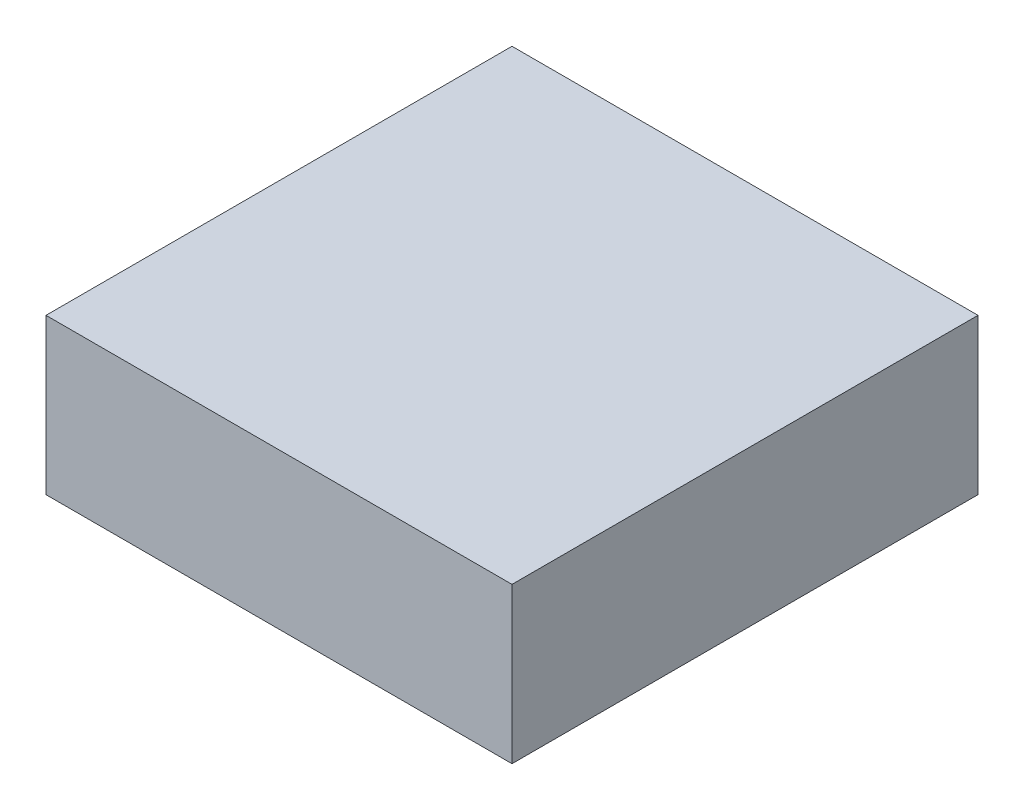
SolidWorks part; units mm, degrees
ref_plane "Alzado" through (0, 0, 0) normal (0, 0, 1) x (1, 0, 0)
ref_plane "Planta" through (0, 0, 0) normal (0, 1, 0) x (1, 0, 0)
ref_plane "Vista lateral" through (0, 0, 0) normal (1, 0, 0) x (0, 0, -1)
sketch "Croquis1" plane through (0, 0, 0) normal (0, 1, 0) x (1, 0, 0)
  line L1 (-7.5, -7.5) -> (7.5, -7.5)
  line L2 (-7.5, -7.5) -> (-7.5, 7.5)
  line L3 (-7.5, 7.5) -> (7.5, 7.5)
  line L4 (7.5, -7.5) -> (7.5, 7.5)
  line L5 (-7.5, -7.5) -> (7.5, 7.5) construction
  line L6 (-7.5, 7.5) -> (7.5, -7.5) construction
  point P0 (0, 0)
  dimension "D1" = 15
  dimension "D2" = 15
extrude "Saliente-Extruir1" add sketch "Croquis1" along normal blind 5
